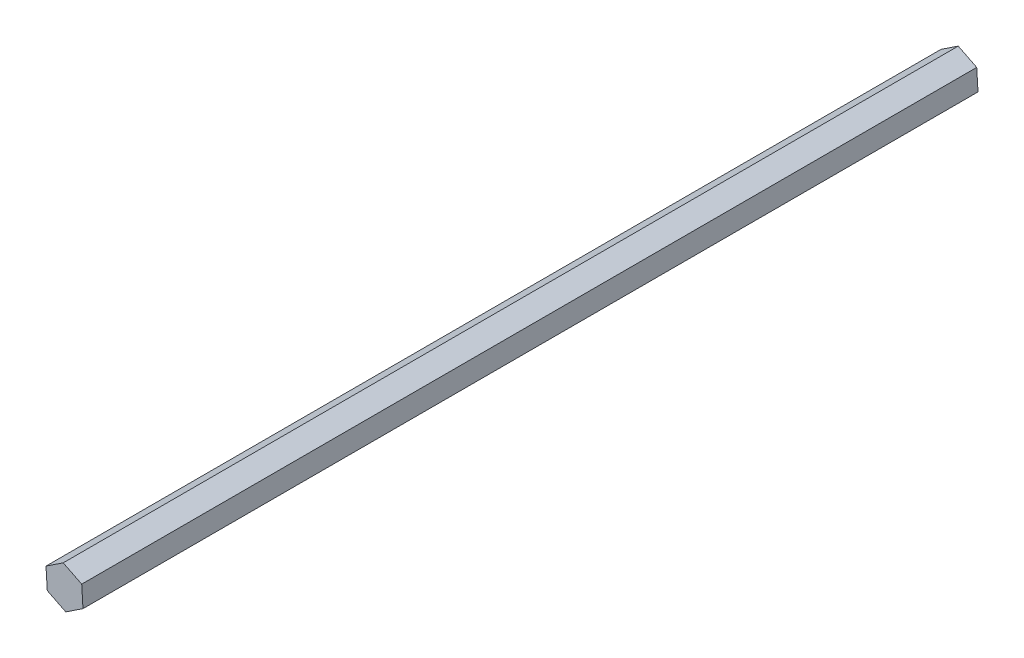
SolidWorks part; units mm, degrees
ref_plane "Front Plane" through (0, 0, 0) normal (0, 0, 1) x (1, 0, 0)
ref_plane "Top Plane" through (0, 0, 0) normal (0, 1, 0) x (1, 0, 0)
ref_plane "Right Plane" through (0, 0, 0) normal (1, 0, 0) x (0, 0, -1)
sketch "Sketch1" plane through (0, 0, 0) normal (0, 0, 1) x (1, 0, 0)
  line L1 (-0.4538, 7.336) -> (-6.58, 3.275)
  line L2 (-6.58, 3.275) -> (-6.1263, -4.061)
  line L3 (-6.1263, -4.061) -> (0.4538, -7.336)
  line L4 (0.4538, -7.336) -> (6.58, -3.275)
  line L5 (6.58, -3.275) -> (6.1263, 4.061)
  line L6 (6.1263, 4.061) -> (-0.4538, 7.336)
  circle A0 centre (0, 0) radius 6.3653 construction
  dimension "D1" = 7.35
extrude "Boss-Extrude1" add sketch "Sketch1" along normal blind 318.55
